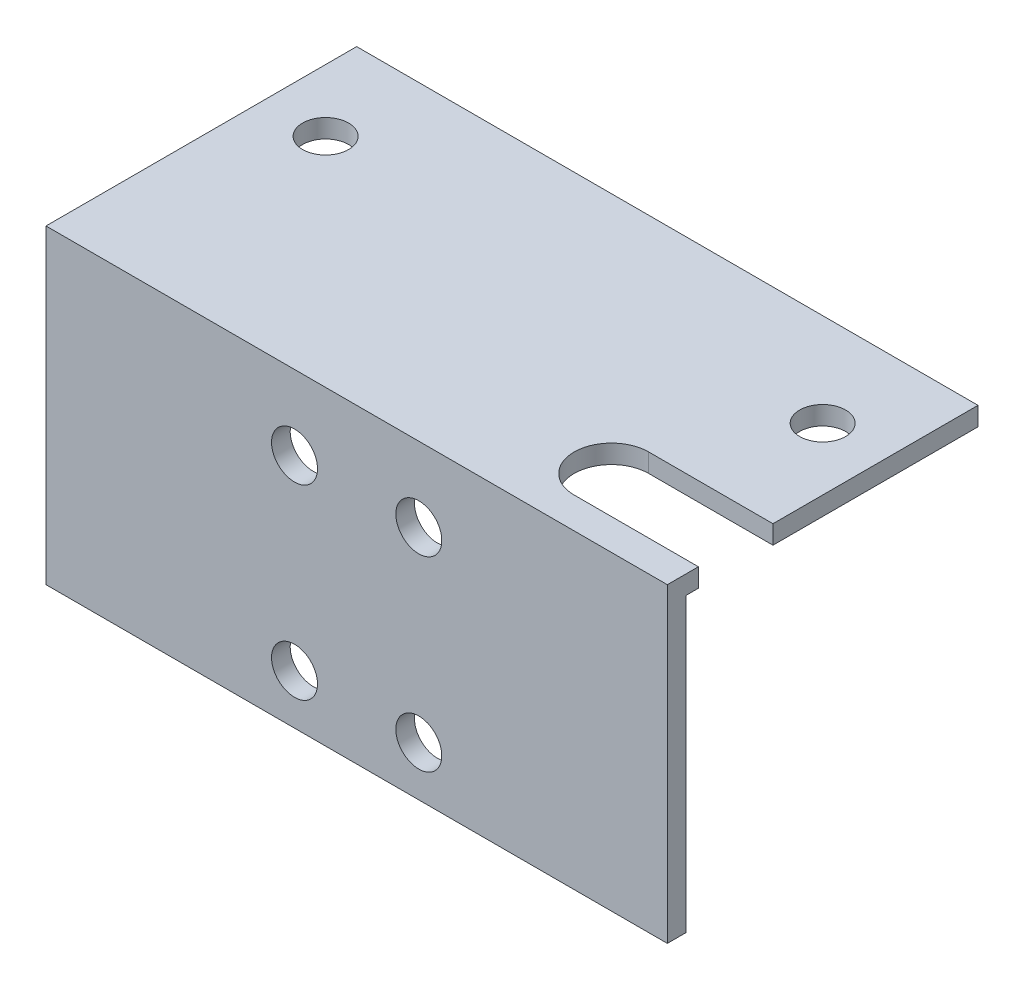
SolidWorks part; units mm, degrees
ref_plane "Front Plane" through (0, 0, 0) normal (0, 0, 1) x (1, 0, 0)
ref_plane "Top Plane" through (0, 0, 0) normal (0, 1, 0) x (1, 0, 0)
ref_plane "Right Plane" through (0, 0, 0) normal (1, 0, 0) x (0, 0, -1)
sketch "Sketch1" plane through (0, 0, 0) normal (0, 1, 0) x (1, 0, 0)
  line L1 (0, 0) -> (50, 0)
  line L2 (0, 0) -> (0, 25)
  line L3 (0, 25) -> (50, 25)
  line L4 (50, 0) -> (50, 25)
  circle A0 centre (5, 17.5) radius 1.85
  circle A1 centre (45, 17.5) radius 1.85
  dimension "D6" = 3.7
  dimension "D1" = 3.7
  dimension "D2" = 25
  dimension "D3" = 17.5
  dimension "D4" = 50
  dimension "D5" = 5
  dimension "D7" = 5
extrude "Boss-Extrude1" add sketch "Sketch1" along normal blind 1.5
sketch "Sketch2" plane through (0, 0, 0) normal (0, -1, 0) x (1, 0, 0)
  line L0 (50, 0) -> (50, -25) construction
  line L1 (0, 0) -> (50, 0)
  line L2 (0, 0) -> (0, -1.5)
  line L3 (0, -1.5) -> (50, -1.5)
  line L4 (50, 0) -> (50, -1.5)
  dimension "D1" = 1.5
extrude "Boss-Extrude2" add sketch "Sketch2" along normal blind 23.5
sketch "Sketch3" plane through (0, 0, -1.5) normal (0, 0, -1) x (-1, 0, 0)
  line L0 (-25, -23.5) -> (-25, 0) construction
  line L1 (0, -23.5) -> (-50, -23.5) construction
  line L2 (0, 0) -> (-50, 0) construction
  circle A0 centre (-20, -19.5) radius 1.85
  circle A1 centre (-30, -19.5) radius 1.85
  circle A2 centre (-20, -4.5) radius 1.85
  circle A3 centre (-30, -4.5) radius 1.85
  dimension "D1" = 3.7
  dimension "D2" = 3.7
  dimension "D3" = 3.7
  dimension "D4" = 3.7
  dimension "D5" = 10
  dimension "D6" = 15
  dimension "D7" = 4
extrude "Cut-Extrude1" cut sketch "Sketch3" against normal blind 23.5
sketch "Sketch4" plane through (0, 0, 0) normal (0, -1, 0) x (1, 0, 0)
  line L0 (50, -5.5) -> (40, -5.5) construction
  line L1 (50, -1.5) -> (50, -25) construction
  line L2 (50, -8.5) -> (40, -8.5)
  line L3 (50, -2.5) -> (40, -2.5)
  arc A0 (50, -8.5) -> (50, -2.5) centre (50, -5.5) ccw
  arc A1 (40, -2.5) -> (40, -8.5) centre (40, -5.5) ccw
  circle A2 centre (45, -17.5) radius 1.85 construction
  point P4 (45, -5.5)
  dimension "D1" = 3
  dimension "D2" = 12
  dimension "D3" = 10
extrude "Cut-Extrude2" cut sketch "Sketch4" against normal blind 10
equation "\"D6@Sketch1\"=\"D1@Sketch1\""
equation "\"D2@Sketch3\"=\"D1@Sketch3\""
equation "\"D3@Sketch3\"=\"D1@Sketch3\""
equation "\"D4@Sketch3\"=\"D1@Sketch3\""
